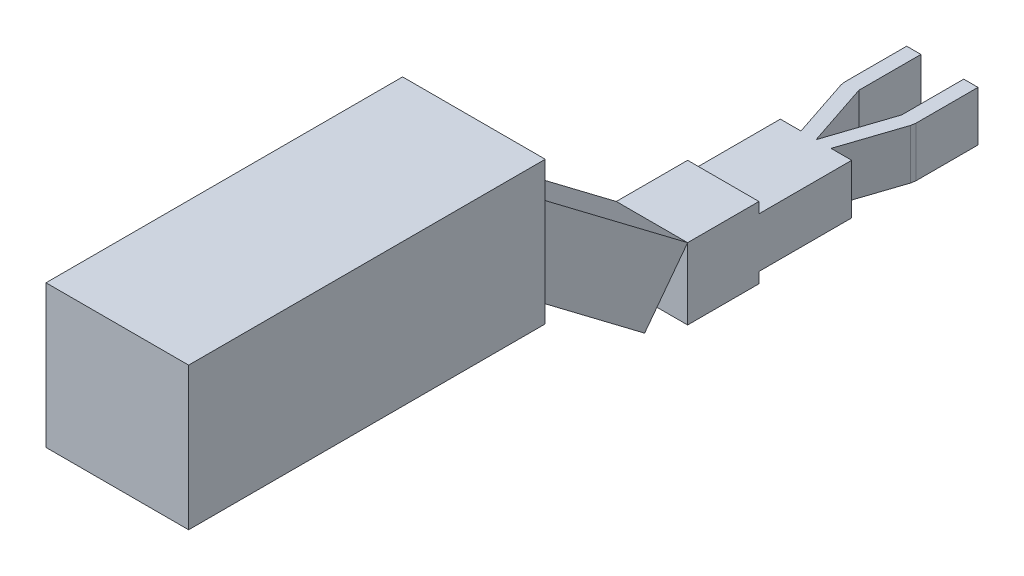
SolidWorks part; units mm, degrees
ref_plane "Front Plane" through (0, 0, 0) normal (0, 0, 1) x (1, 0, 0)
ref_plane "Top Plane" through (0, 0, 0) normal (0, 1, 0) x (1, 0, 0)
ref_plane "Right Plane" through (0, 0, 0) normal (1, 0, 0) x (0, 0, -1)
sketch "Sketch1" plane through (0, 0, 0) normal (0, 1, 0) x (1, 0, 0)
  line L0 (0, -105.7688) -> (-30, -15.63)
  line L1 (-50, 71.37) -> (-30, 71.37)
  line L2 (-50, 71.37) -> (-50, -15.63)
  line L4 (-30, 71.37) -> (-30, -15.63)
  line L5 (30, 71.37) -> (50, 71.37)
  line L6 (30, 71.37) -> (30, -15.63)
  line L8 (50, 71.37) -> (50, -15.63)
  line L9 (21.0786, -105.7688) -> (50, -105.7688)
  line L11 (-21.0786, -105.7688) -> (-48.9766, -21.9458)
  line L12 (0, -105.7688) -> (30, -15.63)
  line L13 (-48.9766, -21.9458) -> (-50, -15.63)
  line L15 (21.0786, -105.7688) -> (48.9766, -21.9458)
  line L16 (-30, 0) -> (0, 0) construction
  line L17 (0, 0) -> (30, 0) construction
  line L18 (50, -15.63) -> (48.9766, -21.9458)
  line L19 (-50, -105.7688) -> (-21.0786, -105.7688)
  line L20 (-50, -105.7688) -> (-50, -235.7688)
  line L21 (-50, -235.7688) -> (50, -235.7688)
  line L22 (50, -105.7688) -> (50, -235.7688)
  dimension "D1" = 20
  dimension "D2" = 20
  dimension "D3" = 60
  dimension "D4" = 87
  dimension "D5" = 95
  dimension "D6" = 100
  dimension "D7" = 130
  dimension "D8" = 20
  dimension "D9" = 20
extrude "Boss-Extrude1" add sketch "Sketch1" along normal blind 70
sketch "Sketch2" plane through (0, 0, 235.7688) normal (0, 0, 1) x (1, 0, 0)
  line L0 (0, 70) -> (0, 0) construction
  line L1 (50, 85) -> (-50, 85)
  line L2 (50, 85) -> (50, -15)
  line L3 (50, -15) -> (-50, -15)
  line L4 (-50, 85) -> (-50, -15)
  line L5 (-50, 70) -> (50, 70) construction
  line L6 (-50, 0) -> (50, 0) construction
  line L7 (0, 0) -> (50, 35) construction
  line L8 (50, 70) -> (50, 0) construction
  line L9 (50, 35) -> (-50, 35) construction
  line L10 (-50, 70) -> (-50, 0) construction
  line L11 (50, 70) -> (0, 35) construction
  line L12 (0, 35) -> (-50, 0) construction
  line L13 (0, 85) -> (0, -15) construction
  point P23 (0, 35)
  dimension "D1" = 100
  dimension "D2" = 100
extrude "Boss-Extrude2" add sketch "Sketch2" along normal blind 100
sketch "Sketch3" plane through (-50, 0, 0) normal (-1, 0, 0) x (0, 0, 1)
  line L0 (335.7688, 85) -> (396.0621, 5.2208)
  line L1 (335.7688, 85) -> (575.1064, 265.8799)
  line L2 (396.0621, 5.2208) -> (635.3996, 186.1007)
  line L3 (575.1064, 265.8799) -> (635.3996, 186.1007)
  dimension "D1" = 100
  dimension "D2" = 300
extrude "Boss-Extrude3" add sketch "Sketch3" against normal blind 100 separate body
sketch "Sketch4" plane through (-50, 0, 0) normal (-1, 0, 0) x (0, 0, 1)
  line L0 (635.3996, 186.1007) -> (1135.3996, 186.1007)
  line L1 (635.3996, 186.1007) -> (635.3996, 386.1007)
  line L2 (1135.3996, 186.1007) -> (1135.3996, 386.1007)
  line L3 (635.3996, 386.1007) -> (1135.3996, 386.1007)
  dimension "D1" = 200
  dimension "D2" = 500
extrude "Boss-Extrude4" add sketch "Sketch4" against normal blind 200 separate body
